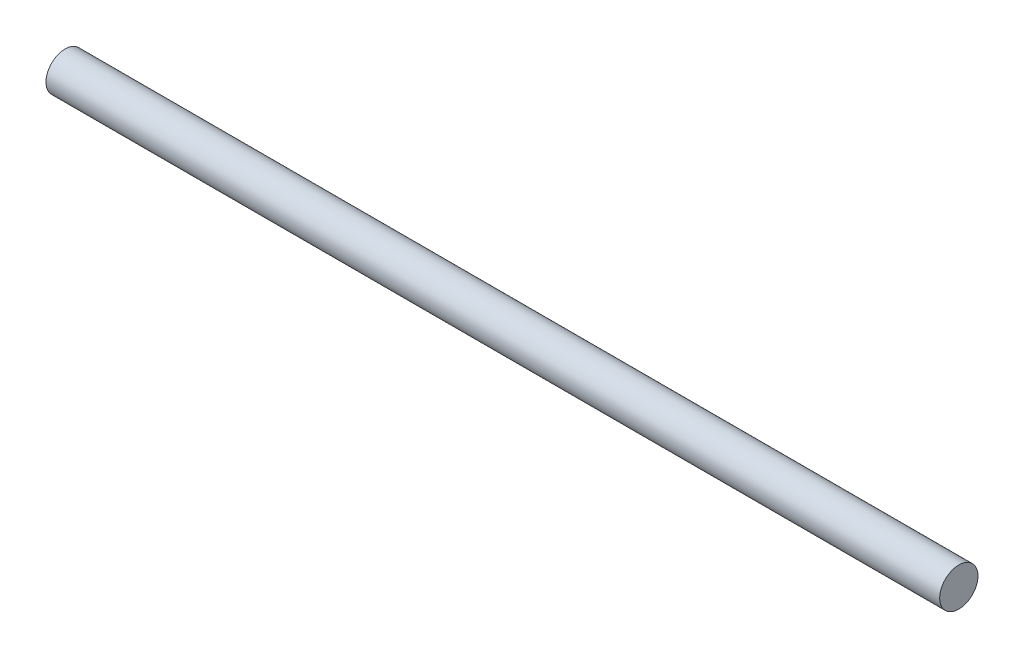
SolidWorks part; units mm, degrees
ref_plane "Front Plane" through (0, 0, 0) normal (0, 0, 1) x (1, 0, 0)
ref_plane "Top Plane" through (0, 0, 0) normal (0, 1, 0) x (1, 0, 0)
ref_plane "Right Plane" through (0, 0, 0) normal (1, 0, 0) x (0, 0, -1)
sketch "Sketch1" plane through (0, 0, 0) normal (1, 0, 0) x (0, 0, -1)
  circle A0 centre (0, 0) radius 1.5
extrude "Boss-Extrude1" add sketch "Sketch1" along normal blind 70
